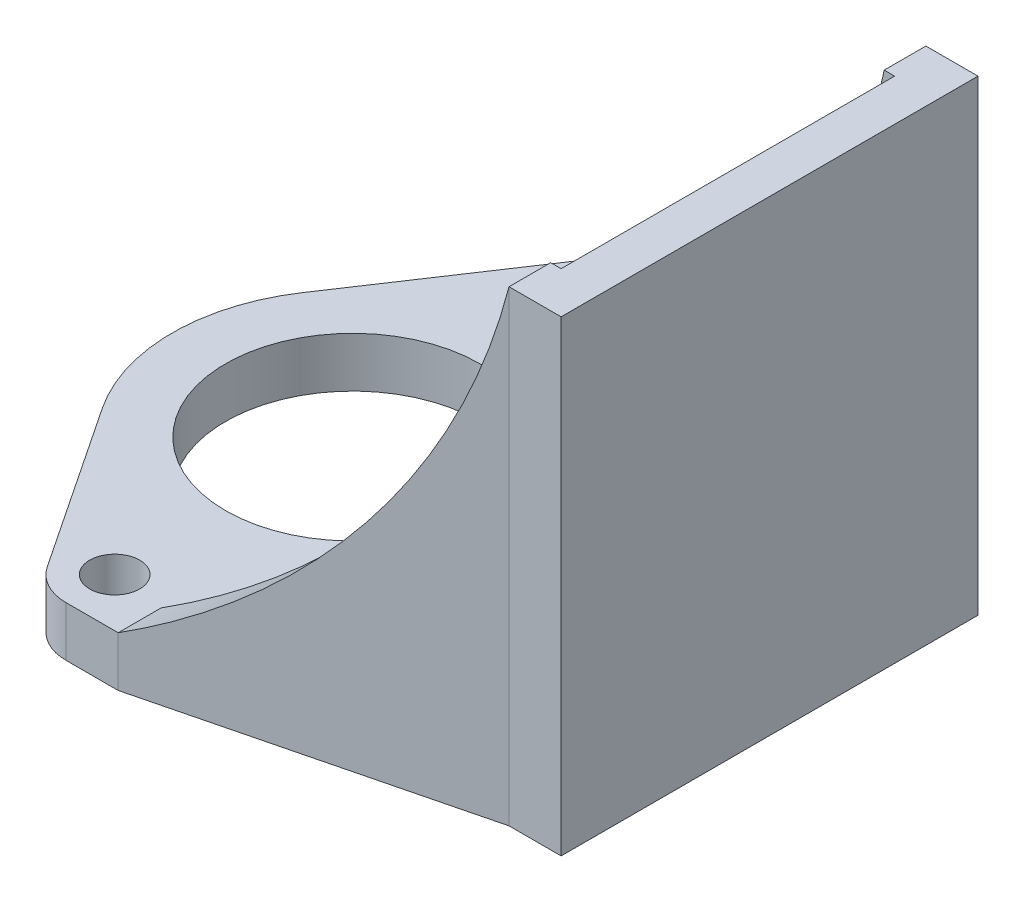
SolidWorks part; units mm, degrees
ref_plane "Front Plane" through (0, 0, 0) normal (0, 0, 1) x (1, 0, 0)
ref_plane "Top Plane" through (0, 0, 0) normal (0, 1, 0) x (1, 0, 0)
ref_plane "Right Plane" through (0, 0, 0) normal (1, 0, 0) x (0, 0, -1)
sketch "Sketch1" plane through (0, 0, 0) normal (0, 1, 0) x (1, 0, 0)
  line L4 (25.4, 12.7) -> (25.4, -12.7)
  line L5 (0, 17.4625) -> (3.175, 17.4625)
  line L7 (0, -17.4625) -> (3.175, -17.4625)
  line L10 (25.4, -12.7) -> (22.225, -12.7)
  line L12 (22.225, 12.7) -> (25.4, 12.7)
  line L13 (3.175, -17.4625) -> (22.225, -12.7)
  line L14 (22.225, 12.7) -> (3.175, 17.4625)
  line L15 (-2.4657, -16.1421) -> (-9.1554, -6.0974)
  line L16 (-9.1554, 6.0974) -> (-2.4657, 16.1421)
  circle A0 centre (0, 0) radius 7.75
  circle A2 centre (0, 0) radius 14.5 construction
  circle A3 centre (0, 14.5) radius 1.524
  circle A4 centre (0, -14.5) radius 1.524
  arc A6 (0, 17.4625) -> (-2.4657, 16.1421) centre (0, 14.5) ccw
  arc A7 (-9.1554, 6.0974) -> (-9.1554, -6.0974) centre (0, 0) ccw
  arc A8 (-2.4657, -16.1421) -> (0, -17.4625) centre (0, -14.5) ccw
  dimension "D1" = 15.5
  dimension "D5" = 29
  dimension "D6" = 3.048
  dimension "D7" = 12.7
  dimension "D8" = 12.7
  dimension "D4" = 3.175
  dimension "D10" = 22
  dimension "D3" = 34.925
  dimension "D9" = 25.4
extrude "Boss-Extrude1" add sketch "Sketch1" along normal blind 3.048
sketch "Sketch2" plane through (0, 3.048, 0) normal (0, 1, 0) x (1, 0, 0)
  line L5 (3.175, -17.4625) -> (22.225, -12.7) construction
  line L6 (22.225, 12.7) -> (3.175, 17.4625) construction
  line L7 (3.175, 17.4625) -> (3.175, 14.8443)
  line L8 (3.175, -17.4625) -> (3.175, -14.8443)
  line L10 (2.559, -14.9983) -> (21.9123, -10.16)
  line L11 (21.9123, -10.16) -> (22.86, -10.16)
  line L12 (21.9123, 10.16) -> (2.559, 14.9983)
  line L13 (22.86, 10.16) -> (21.9123, 10.16)
  line L14 (22.86, -10.16) -> (22.86, 10.16)
  line L15 (3.175, -14.8443) -> (21.9123, -10.16)
  line L16 (21.9123, -10.16) -> (22.86, -10.16)
  line L17 (21.9123, 10.16) -> (3.175, 14.8443)
  line L18 (22.86, 10.16) -> (21.9123, 10.16)
  line L19 (22.86, -10.16) -> (22.86, 10.16)
  line L29 (3.175, -17.4625) -> (22.225, -12.7)
  line L30 (22.225, -12.7) -> (25.4, -12.7)
  line L31 (25.4, -12.7) -> (25.4, 12.7)
  line L32 (25.4, 12.7) -> (22.225, 12.7)
  line L33 (22.225, 12.7) -> (3.175, 17.4625)
  line L34 (3.175, -17.4625) -> (22.225, -12.7)
  line L35 (22.225, -12.7) -> (25.4, -12.7)
  line L36 (25.4, -12.7) -> (25.4, 12.7)
  line L37 (25.4, 12.7) -> (22.225, 12.7)
  line L38 (22.225, 12.7) -> (3.175, 17.4625)
  dimension "D1" = 2.54
  dimension "D2" = 0
extrude "Boss-Extrude2" add sketch "Sketch2" along normal blind 25.4
sketch "Sketch3" plane through (0, 0, -17.4625) normal (0, 0, -1) x (-1, 0, 0)
  line L1 (-22.225, 28.448) -> (-3.175, 28.448)
  line L2 (-3.175, 28.448) -> (-3.175, 3.048)
  arc A0 (-22.225, 28.448) -> (-3.175, 3.048) centre (15.0081, 36.5291) ccw
  dimension "D1" = 76.2
extrude "Cut-Extrude1" cut sketch "Sketch3" against normal through all
